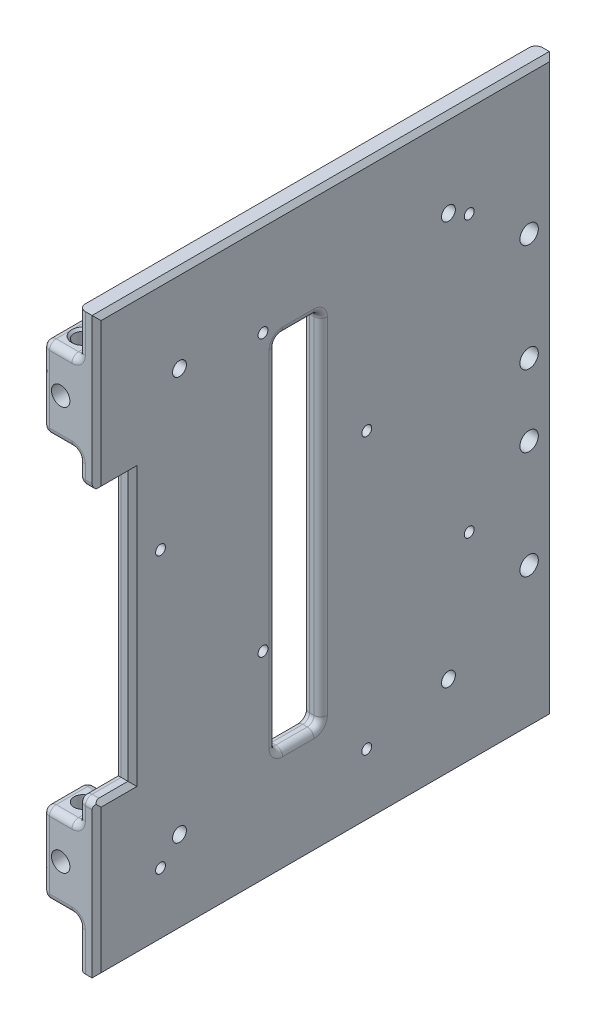
SolidWorks part; units mm, degrees
material "ABS"
ref_plane "Front Plane" through (0, 0, 0) normal (0, 0, 1) x (1, 0, 0)
ref_plane "Top Plane" through (0, 0, 0) normal (0, 1, 0) x (1, 0, 0)
ref_plane "Right Plane" through (0, 0, 0) normal (1, 0, 0) x (0, 0, -1)
sketch "Sketch1" plane through (0, 0, 0) normal (1, 0, 0) x (0, 0, -1)
  line L1 (51, -54) -> (-51, -54)
  line L2 (51, -54) -> (51, 54)
  line L3 (51, 54) -> (-51, 54)
  line L4 (-51, -54) -> (-51, 54)
  line L5 (51, -54) -> (-51, 54) construction
  line L6 (51, 54) -> (-51, -54) construction
  point P0 (0, 0)
  dimension "D1" = 108
  dimension "D2" = 102
extrude "Boss-Extrude1" add sketch "Sketch1" along normal blind 8
sketch "Sketch2" plane through (8, 0, 0) normal (1, 0, 0) x (0, 0, -1)
  line L0 (-51, 0) -> (0, 0) construction
  line L1 (-51, 64) -> (51, 64)
  line L2 (-51, 64) -> (-51, -64)
  line L3 (-51, -64) -> (51, -64)
  line L4 (51, 64) -> (51, -64)
  line L5 (-51, 64) -> (51, -64) construction
  line L6 (-51, -64) -> (51, 64) construction
  line L9 (51, -54) -> (51, 54) construction
  line L10 (-51, 54) -> (-51, -54) construction
  point P0 (0, 0)
  dimension "D1" = 128
extrude "Boss-Extrude2" add sketch "Sketch2" along normal blind 4
sketch "Sketch3" plane through (0, 0, 0) normal (-1, 0, 0) x (0, 0, 1)
  line L0 (51, 54) -> (51, -54) construction
  line L1 (-51, -36) -> (51, -36)
  line L2 (-51, -36) -> (-51, 36)
  line L3 (-51, 36) -> (51, 36)
  line L4 (51, -36) -> (51, 36)
  line L5 (-51, -36) -> (51, 36) construction
  line L6 (-51, 36) -> (51, -36) construction
  line L7 (-51, 54) -> (51, 54) construction
  point P0 (0, 0)
  dimension "D1" = 18
extrude "Cut-Extrude1" cut sketch "Sketch3" against normal up to surface (8 mm away) up to face at (8, 59, 0)
sketch "Sketch5" plane through (0, 0, 0) normal (-1, 0, 0) x (0, 0, 1)
  line L0 (-51, 54) -> (51, 54) construction
  line L1 (-41, -54) -> (41, -54)
  line L2 (-41, -54) -> (-41, 54)
  line L3 (-41, 54) -> (41, 54)
  line L4 (41, -54) -> (41, 54)
  line L5 (-41, -54) -> (41, 54) construction
  line L6 (-41, 54) -> (41, -54) construction
  line L8 (-51, 36) -> (-51, -36) construction
  point P0 (0, 0)
  dimension "D1" = 10
extrude "Cut-Extrude3" cut sketch "Sketch5" against normal up to surface (8 mm away) up to face at (8, 0, 0)
sketch "Sketch6" plane through (12, 0, 0) normal (1, 0, 0) x (0, 0, -1)
  line L0 (-51, 64) -> (-51, -64) construction
  line L1 (-51, -30) -> (-43, -30)
  line L2 (-51, -30) -> (-51, 30)
  line L3 (-51, 30) -> (-43, 30)
  line L4 (-43, -30) -> (-43, 30)
  line L5 (-51, -30) -> (-43, 30) construction
  line L6 (-51, 30) -> (-43, -30) construction
  point P0 (-47, 0)
  dimension "D1" = 8
  dimension "D2" = 60
extrude "Cut-Extrude4" cut sketch "Sketch6" against normal up to surface (4 mm away) up to face at (8, 0, 0)
sketch "Sketch14" plane through (8, 0, 0) normal (-1, 0, 0) x (0, 0, 1)
  line L0 (-51, 36) -> (-51, -36) construction
  line L1 (-41, 36) -> (-51, 36)
  line L2 (-41, 36) -> (-41, 28)
  line L3 (-41, 28) -> (-51, 28)
  line L4 (-51, 36) -> (-51, 28)
  line L6 (-41, -36) -> (-51, -36)
  line L7 (-41, -36) -> (-41, -28)
  line L8 (-41, -28) -> (-51, -28)
  line L9 (-51, -36) -> (-51, -28)
  dimension "D1" = 8
extrude "Boss-Extrude3" add sketch "Sketch14" along normal up to surface (8 mm away) up to face at (0, 45, -46)
sketch "Sketch4" plane through (0, -54, 0) normal (0, -1, 0) x (1, 0, 0)
  line L0 (4, 51) -> (4, -51) construction
  line L1 (8, 51) -> (0, 51) construction
  line L2 (8, -51) -> (0, -51) construction
  circle A0 centre (4, 46) radius 2.025
  circle A1 centre (4, -46) radius 2.025
  dimension "D1" = 4.05
  dimension "D2" = 4.05
  dimension "D3" = 5
  dimension "D4" = 5
extrude "Cut-Extrude2" cut sketch "Sketch4" against normal through all
sketch "Sketch7" plane through (12, 0, 0) normal (1, 0, 0) x (0, 0, -1)
  line L0 (-51, -30) -> (-51, -64) construction
  line L1 (-1, -40) -> (-11, -40)
  line L2 (-1, -40) -> (-1, 40)
  line L3 (-1, 40) -> (-11, 40)
  line L4 (-11, -40) -> (-11, 40)
  line L5 (-1, -40) -> (-11, 40) construction
  line L6 (-1, 40) -> (-11, -40) construction
  line L7 (-4, 0) -> (1, 0) construction
  line L8 (51, -64) -> (51, 64) construction
  line L9 (45.5, 32) -> (45.5, -32) construction
  circle A0 centre (45.5, -32) radius 2.05
  circle A1 centre (45.5, 32) radius 2.05
  circle A2 centre (45.5, 8) radius 2.05
  circle A3 centre (45.5, -8) radius 2.05
  point P0 (-6, 0)
  dimension "D4" = 64
  dimension "D5" = 5.5
  dimension "D6" = 4.1
  dimension "D7" = 4.1
  dimension "D8" = 16
  dimension "D1" = 50
  dimension "D2" = 10
  dimension "D3" = 80
extrude "Cut-Extrude5" cut sketch "Sketch7" against normal up to surface (12 mm away) up to face at (0, 41, -46)
sketch "Sketch11" plane through (0, 0, 51) normal (0, 0, 1) x (1, 0, 0)
  line L0 (0, 54) -> (8, 36) construction
  line L1 (0, 54) -> (0, 36) construction
  line L2 (0, 36) -> (8, 54) construction
  line L3 (0, -36) -> (8, -54) construction
  line L4 (8, -54) -> (0, -54) construction
  line L5 (0, -54) -> (8, -36) construction
  line L6 (8, 54) -> (8, 30) construction
  line L7 (0, 36) -> (8, 36) construction
  line L8 (8, 54) -> (0, 54) construction
  line L9 (0, -36) -> (0, -54) construction
  line L10 (8, -36) -> (0, -36) construction
  line L11 (8, -30) -> (8, -54) construction
  circle A0 centre (4, 45) radius 2.05
  circle A1 centre (4, -45) radius 2.05
  dimension "D1" = 4.1
  dimension "D2" = 4.1
  dimension "D3" = 9
  dimension "D4" = 9
extrude "Cut-Extrude8" cut sketch "Sketch11" against normal blind 3.5
chamfer "Chamfer1" distance 1 angle 45 8 edges at (12, -30, 47) (12, 0, 43) (12, 30, 47) (12, -47, 51) (12, -64, 0) (12, 0, -51) (12, 64, 0) (12, 47, 51)
fillet "Fillet2" radius 1.5 15 edges at (10, 40, 11) (10, 40, 1) (12, 40, 6) (8, 40, 6) (8, 0, 11) (12, 0, 11) (10, -40, 11) (10, -40, 1) (8, 0, 1) (12, 0, 1) (8, -40, 6) (12, -40, 6) (8, -30, 47) (8, 30, 47) (8, 0, 43)
chamfer "Chamfer2" distance 0.5 angle 45 4 edges at (4, 54, 43.975) (4, 54, -48.025) (4, -54, -48.025) (4, -54, 43.975)
fillet "Fillet3" radius 1.5 55 edges at (8, 59, -51) (8, 41, -41) (0, 41, -41) (8, 54, -46) (0, 36, 46) (8, 36, 46) (0, 54, -46) (0, 41, -51) (4, 54, -51) (4, 54, -41) (10.25, 30, 51) (10.25, -30, 51) (8.4393, 30.4393, 51) (8.4393, -30.4393, 51) (8, 33.75, 51) (8, 59, 51) (8, -33.75, 51) (8, -59, 51) (8, -59, -51) (0, 45, 41) (8, 45, 41) (4, 36, 41) (4, 36, 51) (4, 54, 41) (8, 54, 46) (4, 54, 51) (0, 45, 51) (0, 54, 46) (4, -36, 51) (4, -36, 41) (0, -45, 41) (8, -45, 41) (4, -54, 41) (0, -54, 46) (8, -54, 46) (4, -54, 51) (0, -45, 51) (4, -54, -51) (0, -41, -51) (0, -41, -41) (8, -41, -41) (8, -36, 46) (0, -36, 46) (4, -54, -41) (8, -54, -46) (0, -54, -46) (4, -28, -51) (8, 0, -51) (4, 28, -41) (4, -28, -41) (8, -28, -46) (8, 28, -46) (4, 28, -51) (0, 28, -46) (0, -28, -46)
sketch "Sketch8" plane through (12, 0, 0) normal (1, 0, 0) x (0, 0, -1)
  line L0 (-36.7241, -49.3932) -> (-13.8641, -49.3932) construction
  line L1 (-13.8641, -49.3932) -> (-13.8641, -18.9132) construction
  line L2 (-36.7241, -49.3932) -> (-36.7241, -18.9132) construction
  line L3 (-13.8641, -18.9132) -> (-36.7241, -18.9132) construction
  line L4 (-36.7241, 12.0868) -> (-13.8641, 12.0868) construction
  line L5 (-13.8641, 12.0868) -> (-13.8641, 42.5668) construction
  line L6 (-36.7241, 12.0868) -> (-36.7241, 42.5668) construction
  line L7 (-13.8641, 42.5668) -> (-36.7241, 42.5668) construction
  line L8 (9.2759, -49.3932) -> (32.1359, -49.3932) construction
  line L9 (32.1359, -49.3932) -> (32.1359, -18.9132) construction
  line L10 (9.2759, -49.3932) -> (9.2759, -18.9132) construction
  line L11 (32.1359, -18.9132) -> (9.2759, -18.9132) construction
  line L12 (9.2759, 12.0868) -> (32.1359, 12.0868) construction
  line L13 (32.1359, 12.0868) -> (32.1359, 42.5668) construction
  line L14 (9.2759, 12.0868) -> (9.2759, 42.5668) construction
  line L15 (32.1359, 42.5668) -> (9.2759, 42.5668) construction
  line L16 (-12.5, 0) -> (-32.5, 0) construction
  line L17 (-12.5, -38.5) -> (-12.5, 38.5) construction
  line L18 (-32.5, 45) -> (-32.5, -45) construction
  line L20 (-32.5, -45) -> (27.5, -45) construction
  line L21 (-32.5, 45) -> (27.5, 45) construction
  circle A0 centre (-36.7241, -49.3932) radius 1.1
  circle A1 centre (-13.8641, -18.9132) radius 1.1
  circle A2 centre (-36.7241, 12.0868) radius 1.1
  circle A3 centre (-13.8641, 42.5668) radius 1.1
  circle A4 centre (9.2759, -49.3932) radius 1.1
  circle A5 centre (32.1359, -18.9132) radius 1.1
  circle A6 centre (9.2759, 12.0868) radius 1.1
  circle A7 centre (32.1359, 42.5668) radius 1.1
  circle A8 centre (-32.5, -45) radius 1.55
  circle A9 centre (-32.5, 45) radius 1.55
  circle A10 centre (27.5, -45) radius 1.55
  circle A11 centre (27.5, 45) radius 1.55
  point P8 (-32.5, 0)
  point P24 (-61.6026, 75.5947)
  dimension "D1" = 22.86
  dimension "D3" = 2.2
  dimension "D4" = 2.2
  dimension "D8" = 2.2
  dimension "D9" = 2.2
  dimension "D12" = 2.2
  dimension "D13" = 2.2
  dimension "D17" = 2.2
  dimension "D18" = 2.2
  dimension "D20" = 60
  dimension "D22" = 3.1
  dimension "D25" = 3.1
  dimension "D26" = 3.1
  dimension "D27" = 3.1
  dimension "D2" = 30.48
  dimension "D5" = 22.86
  dimension "D6" = 31
  dimension "D7" = 30.48
  dimension "D10" = 22.86
  dimension "D11" = 30.48
  dimension "D14" = 46
  dimension "D15" = 22.86
  dimension "D16" = 30.48
  dimension "D19" = 46
  dimension "D21" = 20
  dimension "D23" = 45
  dimension "D24" = 90
  dimension "D28" = 60
extrude "Cut-Extrude6" cut sketch "Sketch8" against normal up to surface (4 mm away) up to face at (8, 0, 4.55)
